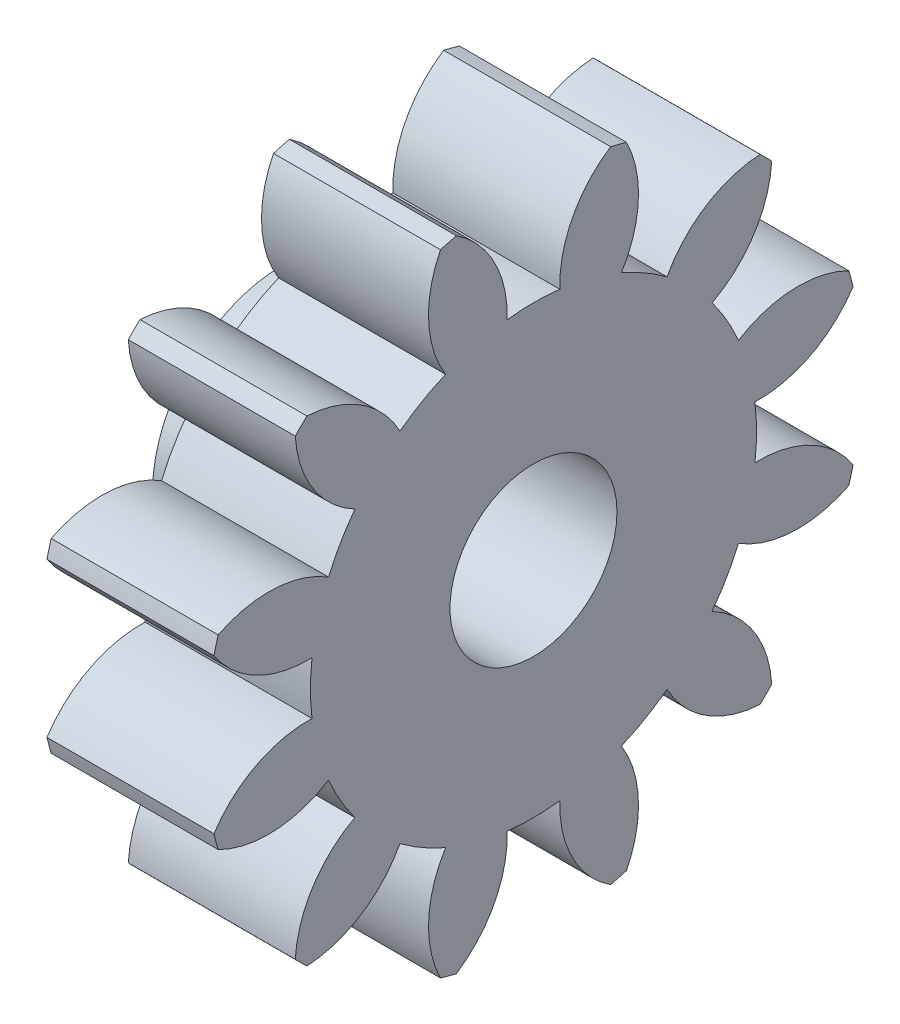
SolidWorks part; units mm, degrees
material "PLA"
ref_plane "Plane1" through (0, 0, 0) normal (0, 0, 1) x (1, 0, 0)
ref_plane "Plane2" through (0, 0, 0) normal (0, 1, 0) x (1, 0, 0)
ref_plane "Plane3" through (0, 0, 0) normal (1, 0, 0) x (0, 0, -1)
other "Configuration Table"
sketch "HoldingSke" plane through (0, 0, 0) normal (0, 1, 0) x (1, 0, 0)
  line L0 (0, 0) -> (0.8695, -0.1848)
  line L1 (-15, 0) -> (100, 0) construction
  line L2 (0, 0) -> (-2.1039, 2.3779)
  line L3 (0, 0) -> (-11.863, 4.5341)
  line L4 (0, 0) -> (8.4473, 1.7955)
  line L5 (0, 0) -> (-46.8476, -17.4728)
  line L6 (0, 0) -> (-3.3159, -2.2372)
  line L7 (-2.1039, 2.3779) -> (8.6586, 51.2059)
  line L8 (-76.2, 54.61) -> (-75.7, 54.61)
  line L9 (-71.009, 38.7566) -> (-53.1078, 45.2721)
  line L10 (-76.2, 71.12) -> (104.1128, 71.12)
  line L11 (0, 0) -> (-4, 0)
  line L12 (-76.2, 101.6) -> (-76.158, 101.6)
  line L13 (24.9733, 27.94) -> (52.9518, 28.4284)
  line L14 (24.9733, 27.94) -> (24.9743, 27.94)
  line L15 (24.9733, 27.94) -> (100.4006, 29.5858)
  line L16 (-63.627, -1.125) -> (-12.827, -1.125)
  circle A0 centre (0, 0) radius 1.5
  circle A1 centre (0, 0) radius 5.3427
  circle A2 centre (0, 0) radius 37.5
  circle A3 centre (0, 0) radius 1.5
  dimension "MHD" = 10.6855
  dimension "Hub_dia" = 75
  dimension "Bore" = 3
  dimension "MBD" = 3
  dimension "Num_teeth" = 12
  dimension "Pitch" = 0.8889
  dimension "Overall_len" = 50
  dimension "Show_teeth" = 12
  dimension "Thickness" = 4
  dimension "OAL" = 50.0001
  dimension "T_dim" = 0.5
  dimension "Ap" = 20
  dimension "H" = 19.05
  dimension "Pitch_radius" = 180.3128
  dimension "Width" = 4
  dimension "Backlash" = 0.042
  dimension "Addendum_fac" = 1
  dimension "Dedendum_fac" = 1.25
  dimension "Clearance_fac" = 0.25
  dimension "Dedendum_add" = 0.001
  dimension "Module" = 1.125
sketch "BasProSke" plane through (0, 0, 0) normal (0, 1, 0) x (1, 0, 0)
  line L0 (-10, 0) -> (60, 0) construction
  line L1 (0, 0) -> (0, 7.875)
  line L2 (0, 0) -> (4, 0)
  line L3 (4, 0) -> (4, 7.875)
  line L4 (4, 7.875) -> (0, 7.875)
  dimension "Thickness" = 4
  dimension "Diameter" = 15.75
revolve "Base-Revolve" add sketch "BasProSke" angle 360 about L0
sketch "TooCutSke" plane through (0, 0, 0) normal (1, 0, 0) x (0, 0, -1)
  line L1 (0, 0) -> (0, 107) construction
  line L2 (0, 0) -> (-0.9544, 6.6822) construction
  line L3 (0, 0) -> (-3.469, 12.9463) construction
  line L4 (-0.9544, 6.6822) -> (-1.7345, 6.4732) construction
  arc A0 (0.6314, 5.3053) -> (-0.6314, 5.3053) centre (0, 0) ccw
  arc A1 (1.8767, 7.6743) -> (-1.8767, 7.6743) centre (0, 0) ccw
  circle A2 centre (0, 0) radius 6.75 construction
  circle A3 centre (0, 0) radius 6.3429 construction
  arc A4 (-0.6314, 5.3053) -> (-1.8767, 7.6743) centre (-3.3298, 5.3986) ccw
  arc A5 (1.8767, 7.6743) -> (0.6314, 5.3053) centre (3.3298, 5.3986) ccw
  dimension "Root_dia" = 10.6855
  dimension "Overcut_dia" = 15.8008
  dimension "Pitch_dia" = 13.5
  dimension "Base_dia" = 12.6859
  dimension "Flank_rad" = 2.7
  dimension "Half_ang" = 15
  dimension "Half_CT" = 0.8076
extrude "ToothCut" cut sketch "TooCutSke" along normal through all
fillet "Breaks" [suppressed] radius 0.0225
fillet "RootFillets" [suppressed] radius 0.2823
pattern_circular "TeethCuts" count 12 every 30 about axis through (-10, 0, 0) along (1, 0, 0) of "ToothCut", "RootFillets", "Breaks"
sketch "HubNeaOneSke" plane through (0, 0, 0) normal (-1, 0, 0) x (0, 0, 1)
  circle A0 centre (0, 0) radius 5.3427
  dimension "Diameter" = 10.6855
extrude "HubNearOne" [suppressed] add sketch "HubNeaOneSke" along normal blind 46.0001
sketch "HubNeaBotSke" plane through (0, 0, 0) normal (-1, 0, 0) x (0, 0, 1)
  circle A0 centre (0, 0) radius 5.3427
  dimension "Diameter" = 10.6855
extrude "HubNearBoth" [suppressed] add sketch "HubNeaBotSke" along normal blind 23
ref_plane "FarPln" through (4, 0, 0) normal (1, 0, 0) x (0, 0, -1)
sketch "HubFarSke" plane through (4, 0, 0) normal (1, 0, 0) x (0, 0, -1)
  circle A0 centre (0, 0) radius 5.3427
  dimension "Diameter" = 10.6855
extrude "HubFar" [suppressed] add sketch "HubFarSke" along normal blind 23
sketch "BorSke" plane through (0, 0, 0) normal (1, 0, 0) x (0, 0, -1)
  circle A0 centre (0, 0) radius 1
  dimension "Diameter" = 2
extrude "Bore" cut sketch "BorSke" along normal mid plane 100.0001
sketch "KeySke" plane through (0, 0, 0) normal (1, 0, 0) x (0, 0, -1)
  line L0 (-0.6, 0) -> (-0.6, 2)
  line L1 (-0.6, 2) -> (0.6, 2)
  line L2 (0.6, 2) -> (0.6, 0)
  line L3 (0, 0) -> (0, 34) construction
  line L4 (-0.6, 0) -> (0.6, 0)
  dimension "Offset" = 2
  dimension "Width" = 1.2
extrude "Keyway" [suppressed] cut sketch "KeySke" along normal mid plane 100.0001
pattern_circular "Keyway2" [suppressed] count 2 every 90 about axis through (-10, 0, 0) along (1, 0, 0)
sketch "Sketch1" plane through (0, 0, 0) normal (-1, 0, 0) x (0, 0, 1)
  circle A0 centre (0, 0) radius 2.125
  circle A1 centre (0, 0) radius 3.125
  dimension "D1" = 4.25
  dimension "D2" = 1
extrude "Boss-Extrude1" add sketch "Sketch1" along normal blind 2
sketch "Sketch2" plane through (4, 0, 0) normal (1, 0, 0) x (0, 0, -1)
  circle A0 centre (0, 0) radius 2
  dimension "D1" = 4
extrude "Cut-Extrude1" cut sketch "Sketch2" against normal offset from surface (3 mm away) 3 up to face at (-2, 0, 3.125)
equation "' \"Module@HoldingSke\" = 6.35"
equation "' \"Num_teeth@HoldingSke\" = 12"
equation "' \"Ap@HoldingSke\" =  20"
equation "' \"Ap@HoldingSke\" = 20"
equation "' \"Width@HoldingSke\" = 0.5 * 25.4"
equation "' \"Hub_dia@HoldingSke\"= 1 * 25.4"
equation "' \"Hub_dia@HoldingSke\" = 1 * 25.4"
equation "' \"Overall_len@HoldingSke\" = 1.0 * 25.4"
equation "' \"Bore@HoldingSke\" = 0.75 * 25.4"
equation "' \"T_dim@HoldingSke\" = 0.1 * 25.4"
equation "' \"Width@KeySke\" = 0.25 * 25.4"
equation "' \"Show_teeth@HoldingSke\" = 13"
equation "' \"Backlash@HoldingSke\" = 0.009 * 25.4"
equation "' \"Addendum_fac@HoldingSke\" = 1.0"
equation "' \"Dedendum_fac@HoldingSke\" = 1.25"
equation "' \"Dedendum_add@HoldingSke\" = 0.00005 * 25.4"
equation "' \"Clearance_fac@HoldingSke\" = 0.25"
equation "\"Pitch@HoldingSke\" = 1 / \"Module@HoldingSke\""
equation "\"Overcut_dia@TooCutSke\" = (\"Num_teeth@HoldingSke\" + 2 * \"Addendum_fac@HoldingSke\") / \"Pitch@HoldingSke\" + 0.002 * 25.4"
equation "\"Pitch_dia@TooCutSke\" = \"Num_teeth@HoldingSke\" / \"Pitch@HoldingSke\""
equation "\"Base_dia@TooCutSke\" = \"Num_teeth@HoldingSke\" / \"Pitch@HoldingSke\" * cos((\"Ap@HoldingSke\"  * 3.14159265 / 180))"
equation "\"Root_dia@TooCutSke\" = (\"Num_teeth@HoldingSke\" + 2) / \"Pitch@HoldingSke\" - 2 * (\"Addendum_fac@HoldingSke\" + \"Dedendum_fac@HoldingSke\") / \"Pitch@HoldingSke\" - \"Dedendum_add@HoldingSke\" * 2"
equation "\"Half_ang@TooCutSke\" = 180 / \"Num_teeth@HoldingSke\""
equation "\"Half_CT@TooCutSke\" = \"Num_teeth@HoldingSke\" / \"Pitch@HoldingSke\" * sin((3.14159265 / 2 / \"Num_teeth@HoldingSke\")) / 2 - 7 * \"Backlash@HoldingSke\" / 4"
equation "\"Flank_rad@TooCutSke\" = \"Num_teeth@HoldingSke\" / \"Pitch@HoldingSke\" / 5"
equation "\"Radius@RootFillets\" = \"Clearance_fac@HoldingSke\" / \"Pitch@HoldingSke\" + \"Dedendum_add@HoldingSke\""
equation "\"Break_rad@Breaks\" = 0.02 / \"Pitch@HoldingSke\""
equation "\"Thickness@HoldingSke\" = \"Width@HoldingSke\""
equation "\"OAL@HoldingSke\" = \"Thickness@HoldingSke\""
equation "\"MHD@HoldingSke\" = (\"Num_teeth@HoldingSke\" + 2) / \"Pitch@HoldingSke\" - 2 * (\"Addendum_fac@HoldingSke\" + \"Dedendum_fac@HoldingSke\")  / \"Pitch@HoldingSke\" - \"Dedendum_add@HoldingSke\" * 2"
equation "\"MBD@HoldingSke\" = (\"Num_teeth@HoldingSke\" + 2) / \"Pitch@HoldingSke\" - 2 * (\"Addendum_fac@HoldingSke\" + \"Dedendum_fac@HoldingSke\")  / \"Pitch@HoldingSke\" - \"Dedendum_add@HoldingSke\" * 2 - 0.002 * 25.4"
equation "\"MHD@HoldingSke\" = ((sgn( \"MHD@HoldingSke\" - \"Hub_dia@HoldingSke\" )-1)*( \"MHD@HoldingSke\" - \"Hub_dia@HoldingSke\" ))/-2+ \"Hub_dia@HoldingSke\""
equation "\"MBD@HoldingSke\" = ((sgn( \"MBD@HoldingSke\" - \"Bore@HoldingSke\" )-1)*( \"MBD@HoldingSke\" - \"Bore@HoldingSke\" ))/-2+ \"Bore@HoldingSke\""
equation "\"OAL@HoldingSke\" = ((sgn( \"OAL@HoldingSke\" - \"Overall_len@HoldingSke\" )+1)*( \"OAL@HoldingSke\" - \"Overall_len@HoldingSke\" ))/2 + \"Overall_len@HoldingSke\" + 0.000002 * 25.4"
equation "\"Num_teeth@TeethCuts\" = int( \"Show_teeth@HoldingSke\" ) + 1"
equation "\"Num_teeth@TeethCuts\" = ((sgn( \"Num_teeth@TeethCuts\" - \"Num_teeth@HoldingSke\" )-1)*( \"Num_teeth@TeethCuts\" - \"Num_teeth@HoldingSke\" ))/-2+ \"Num_teeth@HoldingSke\""
equation "\"Num_teeth@TeethCuts\" = ((sgn( \"Num_teeth@TeethCuts\" - 2.0)+1)*( \"Num_teeth@TeethCuts\" - 2.0))/2 +2.0"
equation "\"Angle@TeethCuts\" = 360.0 / \"Num_teeth@HoldingSke\""
equation "\"Diameter@BasProSke\" = (\"Num_teeth@HoldingSke\" + 2 * \"Addendum_fac@HoldingSke\") / \"Pitch@HoldingSke\""
equation "\"Thickness@BasProSke\"  = \"Thickness@HoldingSke\""
equation "' \"Fillet_rad@BasProSke\" =  \"Thickness@HoldingSke\" * 0.05"
equation "' \"Fillet_rad@BasProSke\" = \"Thickness@HoldingSke\" * 0.05"
equation "\"MHD@HoldingSke\" = ((sgn( \"MHD@HoldingSke\" - \"Root_dia@TooCutSke\" )-1)*( \"MHD@HoldingSke\" - \"Root_dia@TooCutSke\" ))/-2+ \"Root_dia@TooCutSke\""
equation "\"Diameter@HubNeaOneSke\" = \"MHD@HoldingSke\""
equation "\"Length@HubNearOne\" = \"OAL@HoldingSke\" - \"Thickness@BasProSke\""
equation "\"Diameter@HubNeaBotSke\" = \"MHD@HoldingSke\""
equation "\"Length@HubNearBoth\" = ( \"OAL@HoldingSke\" - \"Thickness@BasProSke\" ) / 2.0"
equation "\"Thickness@FarPln\" = \"Thickness@BasProSke\""
equation "\"Diameter@HubFarSke\" = \"MHD@HoldingSke\""
equation "\"Length@HubFar\" = ( \"OAL@HoldingSke\" - \"Thickness@BasProSke\" ) / 2.0"
equation "\"D1@Bore\" = \"OAL@HoldingSke\" * 2.0"
equation "\"D1@Keyway\" = \"OAL@HoldingSke\" * 2.0"
equation "\"Offset@KeySke\" = \"T_dim@HoldingSke\" + \"MBD@HoldingSke\" / 2.0"
